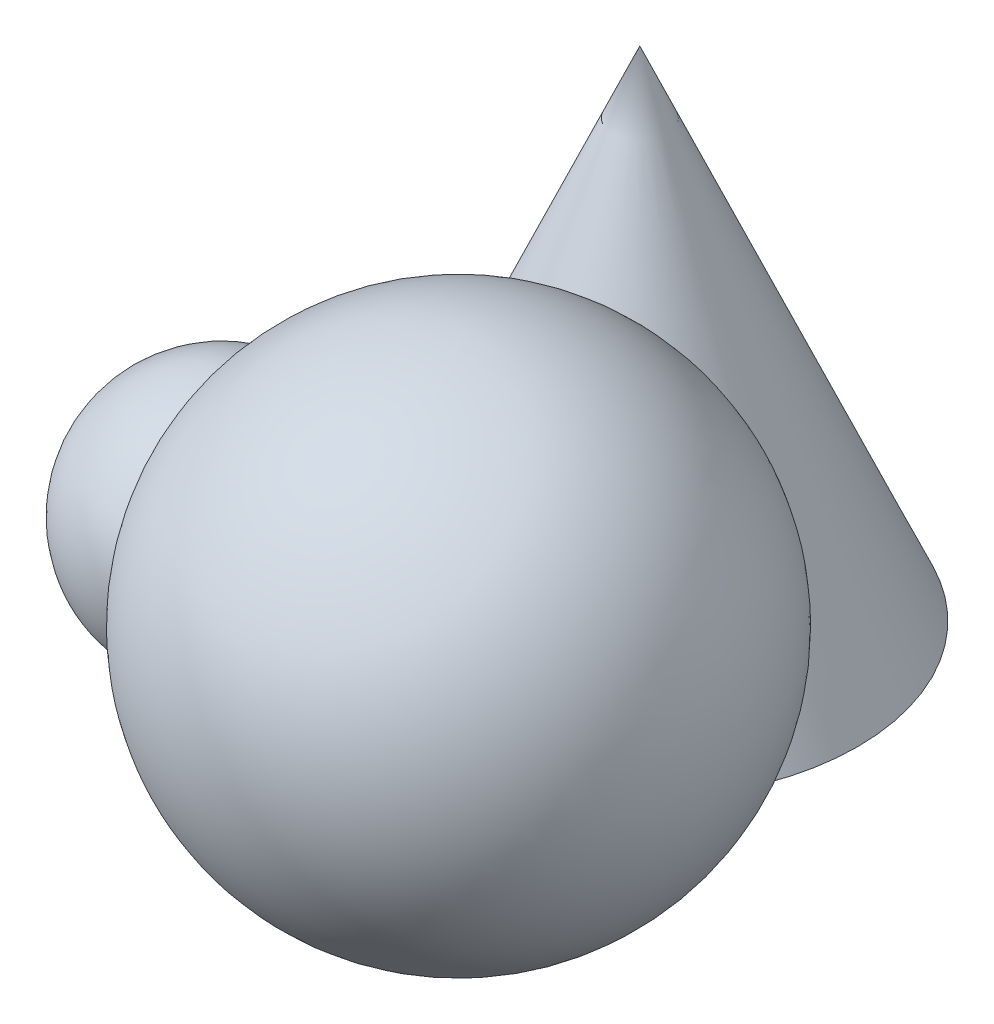
SolidWorks part; units mm, degrees
ref_plane "Front Plane" through (0, 0, 0) normal (0, 0, 1) x (1, 0, 0)
ref_plane "Top Plane" through (0, 0, 0) normal (0, 1, 0) x (1, 0, 0)
ref_plane "Right Plane" through (0, 0, 0) normal (1, 0, 0) x (0, 0, -1)
sketch "Sketch1" plane through (0, 0, 0) normal (0, 0, 1) x (1, 0, 0)
  line L0 (0, 0) -> (35, 0)
  line L1 (35, 0) -> (0, 80)
  line L2 (0, 80) -> (0, 0)
  dimension "D1" = 80
  dimension "D2" = 35
revolve "Revolve1" add sketch "Sketch1" angle 360 about L2
sketch "Sketch2" plane through (0, 0, 0) normal (0, 0, 1) x (1, 0, 0)
  line L0 (0, 0) -> (83.2742, 0) construction
  line L1 (0, 40) -> (83.2742, 40) construction
  line L2 (0, 80) -> (-35, 0) construction
  line L3 (35, 0) -> (0, 80) construction
  circle A0 centre (26.1606, 40) radius 40 construction
  circle A1 centre (61.1606, 40) radius 40 construction
  dimension "D1" = 40
ref_plane "Plane1" through (0, 40, 0) normal (0, 1, 0) x (-1, 0, 0)
sketch "Sketch3" plane through (0, 40, 0) normal (0, 1, 0) x (-1, 0, 0)
  line L0 (-26.1606, 15.2833) -> (-26.1606, 95.2833)
  line L1 (-26.1606, 0) -> (-26.1606, 15.2833) construction
  circle A0 centre (0, 0) radius 61.1606 construction
  arc A1 (-26.1606, 95.2833) -> (-26.1606, 15.2833) centre (-26.1606, 55.2833) ccw
  dimension "D1" = 80
revolve "Revolve2" add sketch "Sketch3" angle 360 about L1
sketch "Sketch5" plane through (0, 0, 0) normal (0, 0, 1) x (1, 0, 0)
  line L0 (-35, 0) -> (-75.0461, 0) construction
  line L1 (0, 80) -> (-35, 0) construction
  circle A0 centre (-48.0803, 20) radius 20 construction
  dimension "D1" = 40
ref_plane "Plane2" through (0, 0, 55.2833) normal (0, 0, 1) x (1, 0, 0)
sketch "Sketch6" plane through (0, 0, 55.2833) normal (0, 0, 1) x (1, 0, 0)
  line L0 (26.1606, 0) -> (-27.3751, 0) construction
  circle A0 centre (26.1606, 40) radius 40 construction
  circle A1 centre (-30.4079, 20) radius 20 construction
  dimension "D1" = 40
ref_plane "Plane3" through (0, 20, 0) normal (0, 1, 0) x (-1, 0, 0)
sketch "Sketch7" plane through (0, 20, 0) normal (0, 1, 0) x (-1, 0, 0)
  line L0 (28.0325, 59.0627) -> (28.0325, 19.0627)
  circle A0 centre (-26.1606, 55.2833) radius 56.5685 construction
  circle A1 centre (0, 0) radius 48.0803 construction
  arc A2 (28.0325, 19.0627) -> (28.0325, 59.0627) centre (28.0325, 39.0627) ccw
  dimension "D1" = 40
revolve "Revolve3" add sketch "Sketch7" angle 360 about L0
